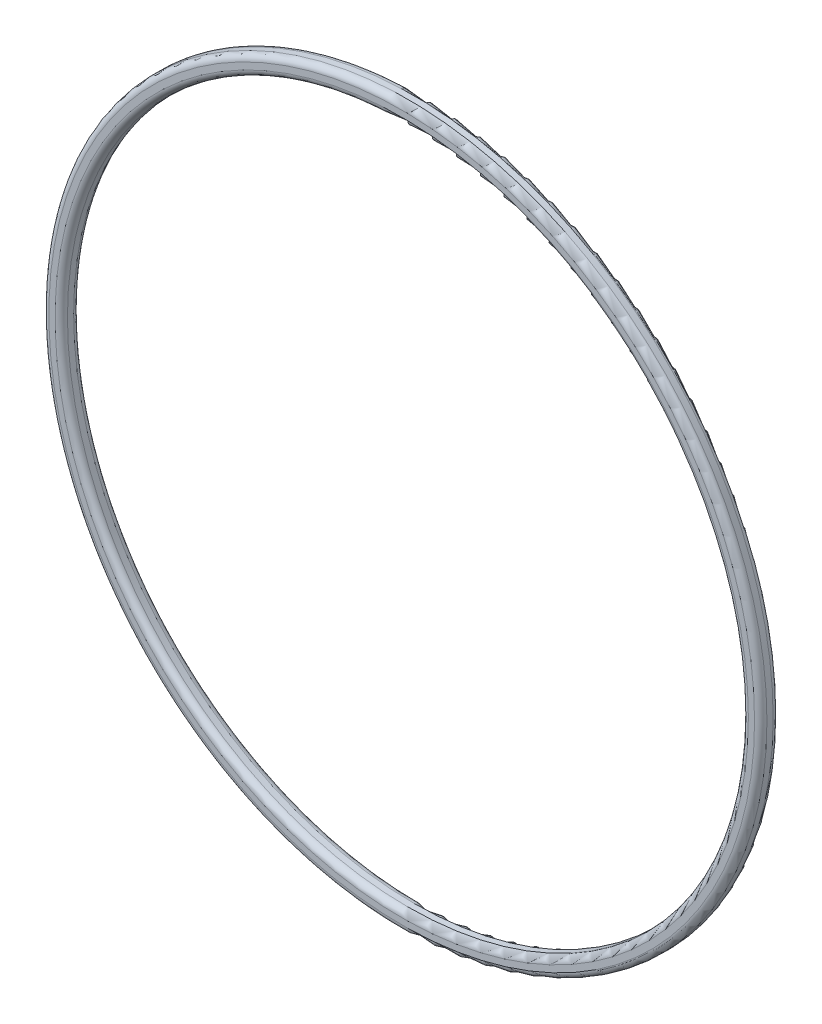
SolidWorks part; units mm, degrees
material "Gomma siliconata"
ref_plane "Piano frontale" through (0, 0, 0) normal (0, 0, 1) x (1, 0, 0)
ref_plane "Piano superiore" through (0, 0, 0) normal (0, 1, 0) x (1, 0, 0)
ref_plane "Piano destro" through (0, 0, 0) normal (1, 0, 0) x (0, 0, -1)
sketch "Schizzo1" plane through (0, 0, 0) normal (0, 0, 1) x (1, 0, 0)
  circle A0 centre (0, 0) radius 55
  circle A1 centre (0, 0) radius 58
  dimension "D1" = 110
  dimension "D2" = 116
extrude "Estrusione-Estrusione1" add sketch "Schizzo1" along normal blind 3
fillet "Raccordo1" radius 1 4 edges at (55, 0, 0) (58, 0, 0) (55, 0, 3) (58, 0, 3)
